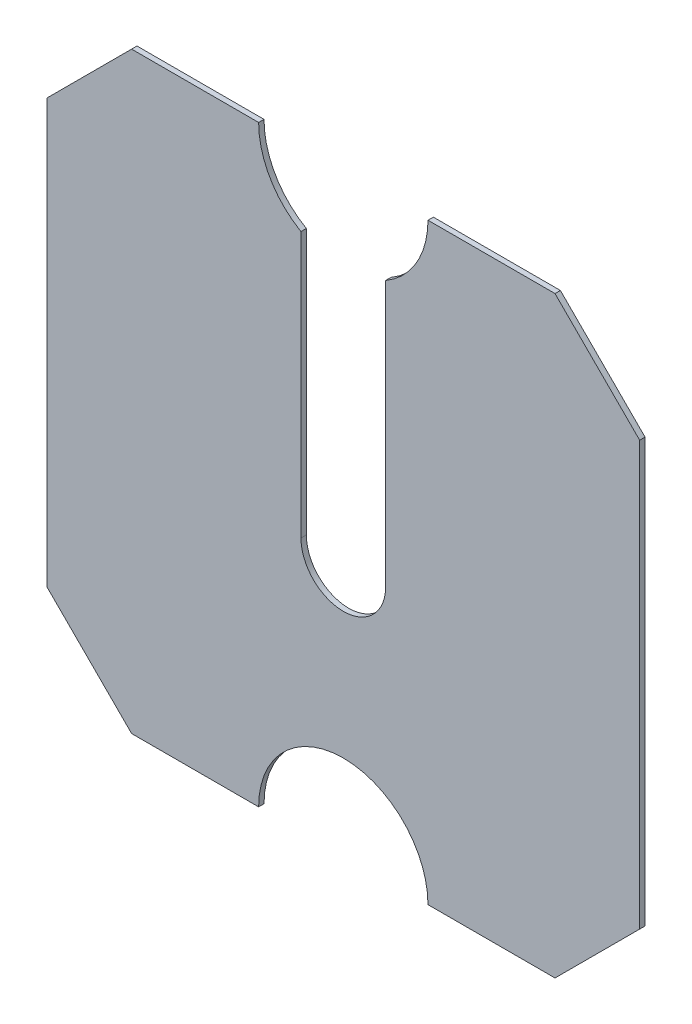
SolidWorks part; units mm, degrees
ref_plane "Front Plane" through (0, 0, 0) normal (0, 0, 1) x (1, 0, 0)
ref_plane "Top Plane" through (0, 0, 0) normal (0, 1, 0) x (1, 0, 0)
ref_plane "Right Plane" through (0, 0, 0) normal (1, 0, 0) x (0, 0, -1)
sketch "Sketch1" plane through (0, 0, 0) normal (0, 0, 1) x (1, 0, 0)
  line L0 (0, 50) -> (0, 300) construction
  line L1 (-175, 175) -> (175, 175) construction
  line L3 (175, 300) -> (175, 50)
  line L4 (175, 50) -> (125, 0)
  line L5 (125, 0) -> (50, 0)
  line L6 (0, 50) -> (0, 0) construction
  line L7 (-50, 0) -> (50, 0) construction
  line L8 (175, 50) -> (175, 0) construction
  line L9 (175, 0) -> (125, 0) construction
  line L10 (175, 350) -> (125, 350) construction
  line L11 (175, 300) -> (175, 350) construction
  line L12 (-50, 350) -> (50, 350) construction
  line L13 (0, 300) -> (0, 350) construction
  line L14 (125, 350) -> (50, 350)
  line L15 (175, 300) -> (125, 350)
  line L16 (-175, 300) -> (-175, 350) construction
  line L17 (-175, 350) -> (-125, 350) construction
  line L18 (-175, 0) -> (-125, 0) construction
  line L19 (-175, 50) -> (-175, 0) construction
  line L20 (-175, 300) -> (-125, 350)
  line L21 (-125, 350) -> (-50, 350)
  line L22 (-125, 0) -> (-50, 0)
  line L23 (-175, 50) -> (-125, 0)
  line L24 (-175, 300) -> (-175, 50)
  arc A0 (50, 0) -> (-50, 0) centre (0, 0) ccw
  arc A1 (50, 350) -> (-50, 350) centre (0, 350) cw
  point P3 (0, 0)
  point P5 (0, 0)
  point P10 (0, 0)
  point P26 (0, 175)
  dimension "D2" = 175
  dimension "D3" = 175
  dimension "D1" = 50
extrude "Boss-Extrude1" add sketch "Sketch1" along normal blind 3.175
sketch "Sketch2" plane through (0, 0, 3.175) normal (0, 0, 1) x (1, 0, 0)
  line L0 (-25, 306.6987) -> (-25, 150)
  line L1 (-25, 150) -> (25, 150) construction
  line L2 (25, 150) -> (25, 306.6987)
  line L3 (125, 350) -> (50, 350) construction
  arc A0 (-50, 350) -> (50, 350) centre (0, 350) ccw construction
  arc A1 (-25, 150) -> (25, 150) centre (0, 150) ccw
  arc A2 (-25, 306.6987) -> (25, 306.6987) centre (0, 350) ccw
  point P8 (25, 306.6987)
  point P9 (0, 0)
  dimension "D1" = 50
  dimension "D2" = 200
extrude "Cut-Extrude1" cut sketch "Sketch2" against normal blind 3.175
equation "\"D3@Sketch1\"=350/2mm"
equation "\"D2@Sketch1\"=350/2mm"
